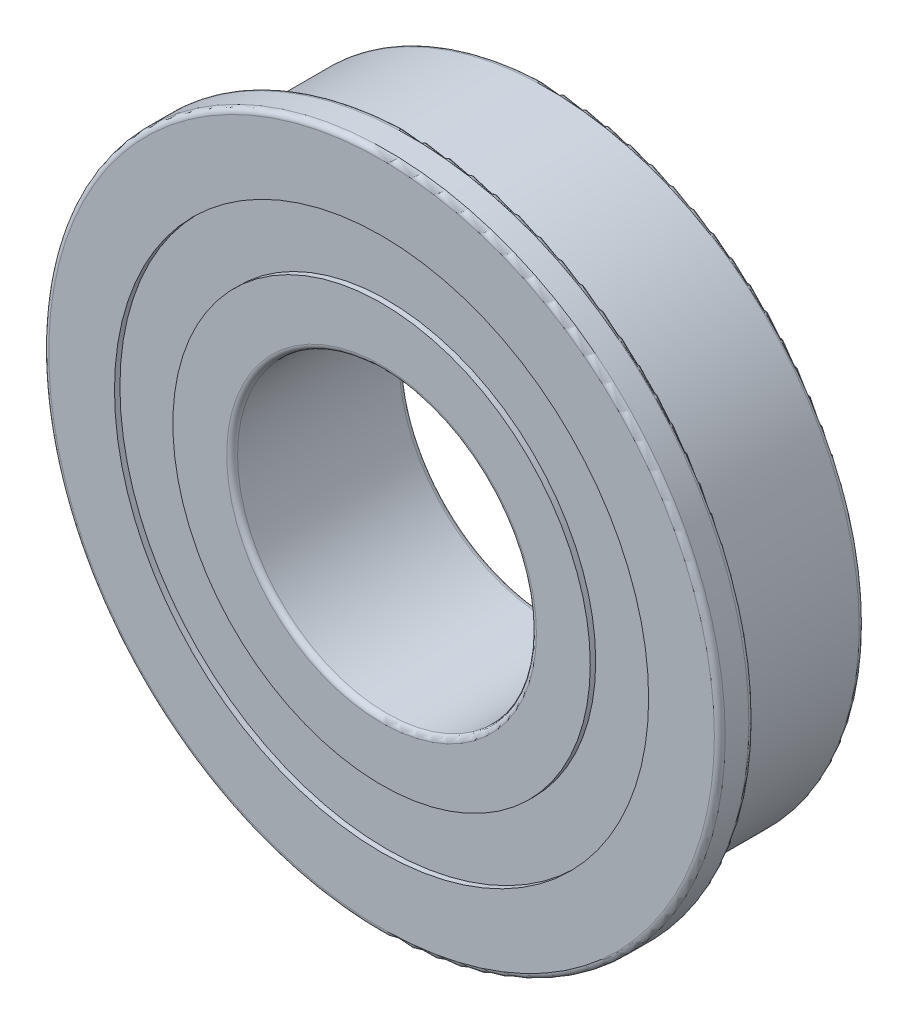
SolidWorks part; units mm, degrees
material "Plain Carbon Steel"
ref_plane "Front Plane" through (0, 0, 0) normal (0, 0, 1) x (1, 0, 0)
ref_plane "Top Plane" through (0, 0, 0) normal (0, 1, 0) x (1, 0, 0)
ref_plane "Right Plane" through (0, 0, 0) normal (1, 0, 0) x (0, 0, -1)
sketch "Sketch1" plane through (0, 0, 0) normal (0, 1, 0) x (1, 0, 0)
  line L0 (14.0375, 3.9688) -> (12.2875, 3.9688)
  line L1 (12.2875, 3.9688) -> (12.2875, 3.7188)
  line L2 (12.2875, 3.7188) -> (9.602, 3.7188)
  line L3 (9.602, 3.7188) -> (9.602, 3.9688)
  line L4 (9.602, 3.9688) -> (7.125, 3.9688)
  line L5 (6.875, 3.7188) -> (6.875, -3.7188)
  line L6 (7.125, -3.9688) -> (9.602, -3.9688)
  line L7 (9.602, -3.9688) -> (9.602, -3.7188)
  line L8 (9.602, -3.7188) -> (12.2875, -3.7188)
  line L9 (12.2875, -3.7188) -> (12.2875, -3.9688)
  line L10 (12.2875, -3.9688) -> (15.31, -3.9688)
  line L11 (15.56, -3.7188) -> (15.56, -2.6313)
  line L12 (15.31, -2.3813) -> (14.2875, -2.3813)
  line L13 (14.071, -2.0063) -> (14.2875, -1.6313)
  line L14 (14.2875, -1.6313) -> (14.2875, 3.7188)
  line L15 (0, 3.97) -> (0, -3.97) construction
  arc A0 (7.125, 3.9688) -> (6.875, 3.7188) centre (7.125, 3.7188) ccw
  arc A1 (6.875, -3.7188) -> (7.125, -3.9688) centre (7.125, -3.7188) ccw
  arc A2 (15.31, -3.9688) -> (15.56, -3.7188) centre (15.31, -3.7188) ccw
  arc A3 (15.56, -2.6313) -> (15.31, -2.3813) centre (15.31, -2.6313) ccw
  arc A4 (14.2875, -2.3813) -> (14.071, -2.0063) centre (14.2875, -2.1313) cw
  arc A5 (14.2875, 3.7188) -> (14.0375, 3.9688) centre (14.0375, 3.7188) ccw
revolve "Revolve1" add sketch "Sketch1" angle 360 about L15
